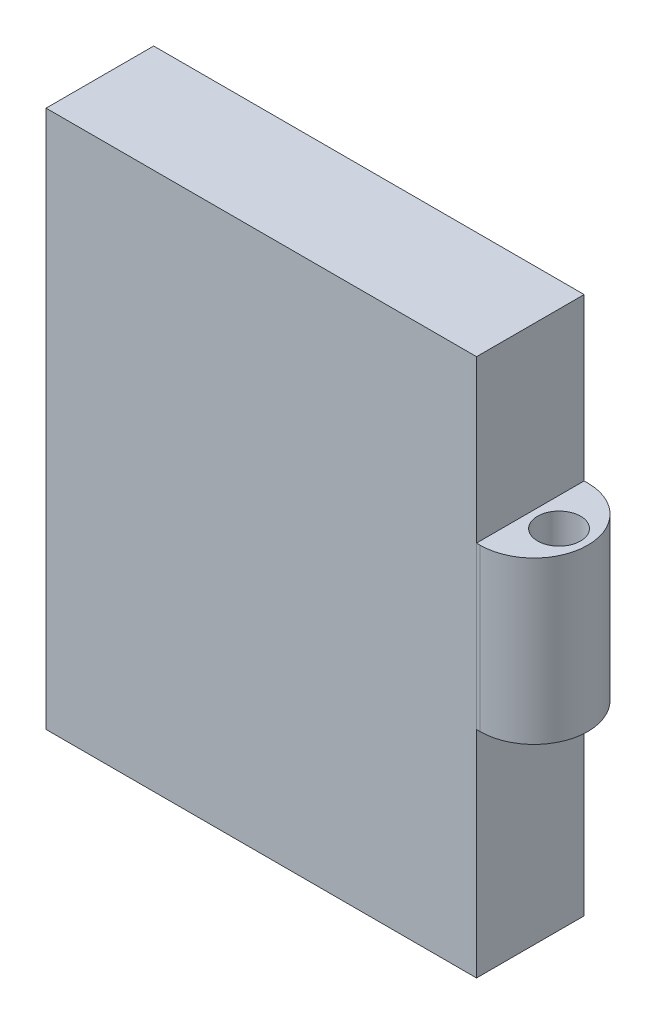
SolidWorks part; units mm, degrees
ref_plane "Front Plane" through (0, 0, 0) normal (0, 0, 1) x (1, 0, 0)
ref_plane "Top Plane" through (0, 0, 0) normal (0, 1, 0) x (1, 0, 0)
ref_plane "Right Plane" through (0, 0, 0) normal (1, 0, 0) x (0, 0, -1)
sketch "Sketch1" plane through (0, 0, 0) normal (0, 0, 1) x (1, 0, 0)
  line L1 (0, 0) -> (40, 0)
  line L2 (0, 0) -> (0, 50)
  line L3 (0, 50) -> (40, 50)
  line L4 (40, 0) -> (40, 50)
  dimension "D1" = 40
  dimension "D2" = 50
extrude "Boss-Extrude1" add sketch "Sketch1" along normal blind 10
shell "Shell4" thickness 3
sketch "Sketch4" plane through (0, 50, 0) normal (0, 1, 0) x (1, 0, 0)
  line L0 (40, 0) -> (40.3371, 0)
  line L1 (40, -5) -> (45.3392, -5.0021) construction
  line L2 (40.3371, -10.0042) -> (40, -10)
  line L6 (40, 0) -> (0, 0)
  line L7 (0, 0) -> (0, -10)
  line L8 (0, -10) -> (40, -10)
  line L9 (40, -10) -> (40, 0)
  line L13 (40, -10) -> (40, 0)
  arc A0 (40.3371, 0) -> (40.3371, -10.0042) centre (40.3371, -5.0021) cw
  circle A1 centre (42.6696, -5.001) radius 2
  dimension "D2" = 4
  dimension "D1" = 0
extrude "Boss-Extrude4" add sketch "Sketch4" against normal blind 15 from offset 15 offset against normal yes
sketch "Sketch9" plane through (0, 0, 0) normal (0, 0, -1) x (-1, 0, 0)
  line L0 (-40, 0) -> (-40, 20) construction
  line L1 (0, 0) -> (-40, 0) construction
  circle A0 centre (-38, 15) radius 0.5
  circle A1 centre (-35, 15) radius 0.5
  circle A2 centre (-32, 15) radius 0.5
  circle A3 centre (-29, 15) radius 0.5
  circle A4 centre (-26, 15) radius 0.5
  circle A5 centre (-35, 12) radius 0.5
  circle A6 centre (-32, 12) radius 0.5
  circle A7 centre (-29, 12) radius 0.5
  circle A8 centre (-26, 12) radius 0.5
  circle A9 centre (-35, 9) radius 0.5
  circle A10 centre (-32, 9) radius 0.5
  circle A11 centre (-29, 9) radius 0.5
  circle A12 centre (-26, 9) radius 0.5
  circle A13 centre (-35, 6) radius 0.5
  circle A14 centre (-32, 6) radius 0.5
  circle A15 centre (-29, 6) radius 0.5
  circle A16 centre (-26, 6) radius 0.5
  circle A17 centre (-35, 3) radius 0.5
  circle A18 centre (-32, 3) radius 0.5
  circle A19 centre (-29, 3) radius 0.5
  circle A20 centre (-26, 3) radius 0.5
  circle A21 centre (-38, 12) radius 0.5
  circle A22 centre (-38, 9) radius 0.5
  circle A23 centre (-38, 6) radius 0.5
  circle A24 centre (-38, 3) radius 0.5
  dimension "D1" = 1
  dimension "D2" = 2
  dimension "D3" = 15
  dimension "D4" = 5
  dimension "D5" = 5
extrude "Cut-Extrude2" cut sketch "Sketch9" against normal blind 5
